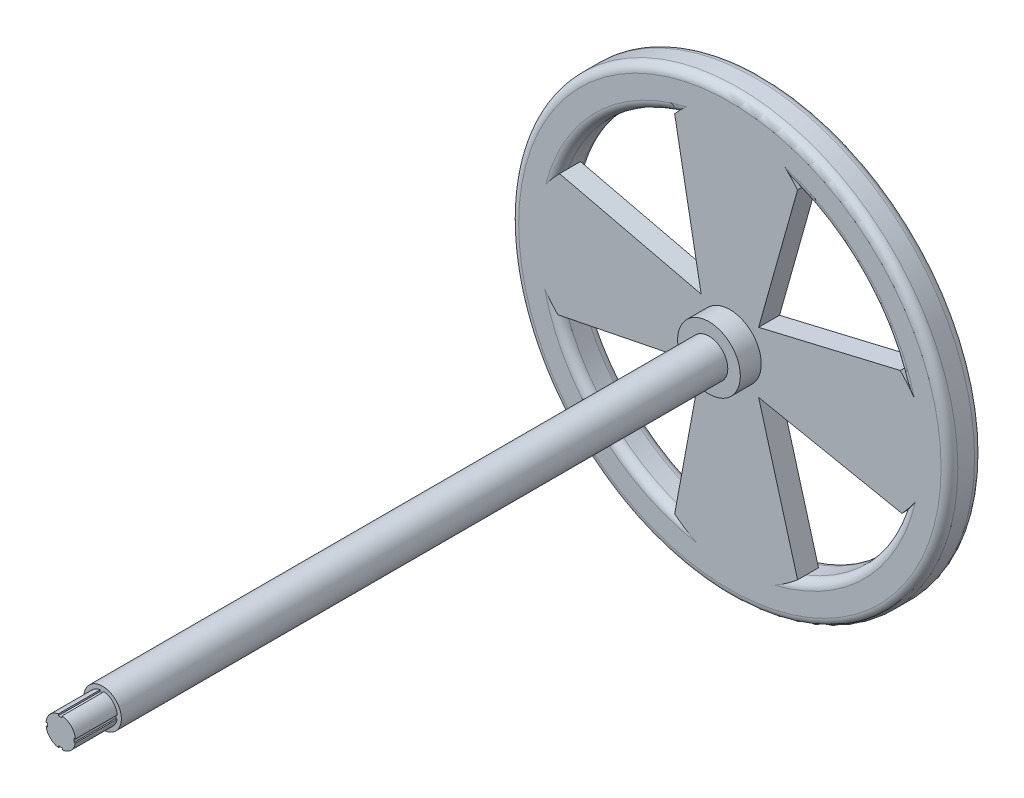
SolidWorks part; units mm, degrees
ref_plane "Front Plane" through (0, 0, 0) normal (0, 0, 1) x (1, 0, 0)
ref_plane "Top Plane" through (0, 0, 0) normal (0, 1, 0) x (1, 0, 0)
ref_plane "Right Plane" through (0, 0, 0) normal (1, 0, 0) x (0, 0, -1)
sketch "Sketch1" plane through (0, 0, 0) normal (0, 0, 1) x (1, 0, 0)
  circle A0 centre (0, 0) radius 133.35
  circle A1 centre (0, 0) radius 110.49
  dimension "D1" = 266.7
  dimension "D2" = 220.98
extrude "Boss-Extrude1" add sketch "Sketch1" along normal blind 20.32
fillet "Fillet1" radius 5.08 1 edges at (133.35, 0, 20.32)
fillet "Fillet4" radius 5.08 1 edges at (133.35, 0, 0)
fillet "Fillet5" radius 5.08 1 edges at (110.49, 0, 20.32)
fillet "Fillet6" radius 5.08 1 edges at (110.49, 0, 0)
sketch "Sketch2" plane through (0, 0, 20.32) normal (0, 0, 1) x (1, 0, 0)
  line L0 (103.4658, 38.767) -> (17.4654, 18.4424) construction
  line L1 (41.1209, 102.553) -> (17.4654, 18.4424) construction
  line L2 (-103.4537, 38.7991) -> (-17.4654, 18.4424) construction
  line L3 (-33.5456, 105.2746) -> (-17.4654, 18.4424) construction
  line L4 (104.4809, -35.9413) -> (17.4654, -18.4424) construction
  line L5 (41.1209, -102.553) -> (17.4654, -18.4424) construction
  line L6 (-33.5456, -105.2746) -> (-17.4654, -18.4424) construction
  line L7 (-104.492, -35.909) -> (-17.4654, -18.4424) construction
  line L8 (103.4658, 38.767) -> (17.4654, 18.4424)
  line L9 (41.1209, 102.553) -> (17.4654, 18.4424)
  line L10 (-33.5456, 105.2746) -> (-17.4654, 18.4424)
  line L11 (-103.4537, 38.7991) -> (-17.4654, 18.4424)
  line L12 (-104.492, -35.909) -> (-17.4654, -18.4424)
  line L13 (-33.5456, -105.2746) -> (-17.4654, -18.4424)
  line L14 (41.1209, -102.553) -> (17.4654, -18.4424)
  line L15 (104.4809, -35.9413) -> (17.4654, -18.4424)
  circle A0 centre (0, 0) radius 110.49 construction
  circle A1 centre (0, 0) radius 25.4
  spline S0 degree 2 poles (104.4809, -35.9413) (139.512, 1.2852) (103.4658, 38.767) knots 0 0 0 1 1 1
  spline S1 degree 2 poles (-33.5456, -105.2746) (3.664, -134.23) (41.1209, -102.553) knots 0 0 0 1 1 1
  spline S2 degree 2 poles (-104.492, -35.909) (-140.4141, 1.2987) (-103.4537, 38.7991) knots 0 0 0 1 1 1
  spline S3 degree 2 poles (-33.5456, 105.2746) (3.0882, 146.6816) (41.1209, 102.553) knots 0 0 0 1 1 1
  dimension "D1" = 50.8
extrude "Boss-Extrude2" add sketch "Sketch2" against normal blind 12.7 separate body
sketch "Sketch3" plane through (0, 0, 20.32) normal (0, 0, 1) x (1, 0, 0)
  circle A0 centre (0, 0) radius 11.43
  dimension "D1" = 22.86
extrude "Boss-Extrude3" add sketch "Sketch3" along normal blind 381
sketch "Sketch4" plane through (0, 0, 401.32) normal (0, 0, 1) x (1, 0, 0)
  line L2 (0.985, -8.9253) -> (0.985, -7.8831)
  line L3 (0.985, -7.8831) -> (-1.301, -7.8831)
  line L4 (-1.301, -8.8848) -> (-1.301, -7.8831)
  line L5 (8.8629, -1.4424) -> (8.1077, -1.4424)
  line L7 (8.9398, 0.8436) -> (8.1077, 0.8436)
  line L8 (8.1077, -1.4424) -> (8.1077, 0.8436)
  line L9 (-8.8531, -1.5018) -> (-8.0385, -1.5018)
  line L11 (-8.9452, 0.7842) -> (-8.0385, 0.7842)
  line L12 (-8.0385, -1.5018) -> (-8.0385, 0.7842)
  line L14 (-1.4494, 8.8618) -> (-1.4494, 7.8772)
  line L15 (-1.4494, 7.8772) -> (0.8366, 7.8772)
  line L16 (0.8366, 8.9405) -> (0.8366, 7.8772)
  arc A0 (8.9398, 0.8436) -> (0.8366, 8.9405) centre (0, 0) ccw
  arc A1 (-1.4494, 8.8618) -> (-8.9452, 0.7842) centre (0, 0) ccw
  arc A2 (-8.8531, -1.5018) -> (-1.301, -8.8848) centre (0, 0) ccw
  arc A3 (0.985, -8.9253) -> (8.8629, -1.4424) centre (0, 0) ccw
  dimension "D1" = 2.286
  dimension "D2" = 2.286
  dimension "D3" = 2.286
  dimension "D4" = 2.286
extrude "Boss-Extrude4" add sketch "Sketch4" along normal blind 25.4
sketch "Sketch5" plane through (0, 0, 20.32) normal (0, 0, 1) x (1, 0, 0)
  circle A0 centre (0, 0) radius 19.05
  dimension "D1" = 38.1
extrude "Boss-Extrude5" add sketch "Sketch5" along normal blind 12.7
